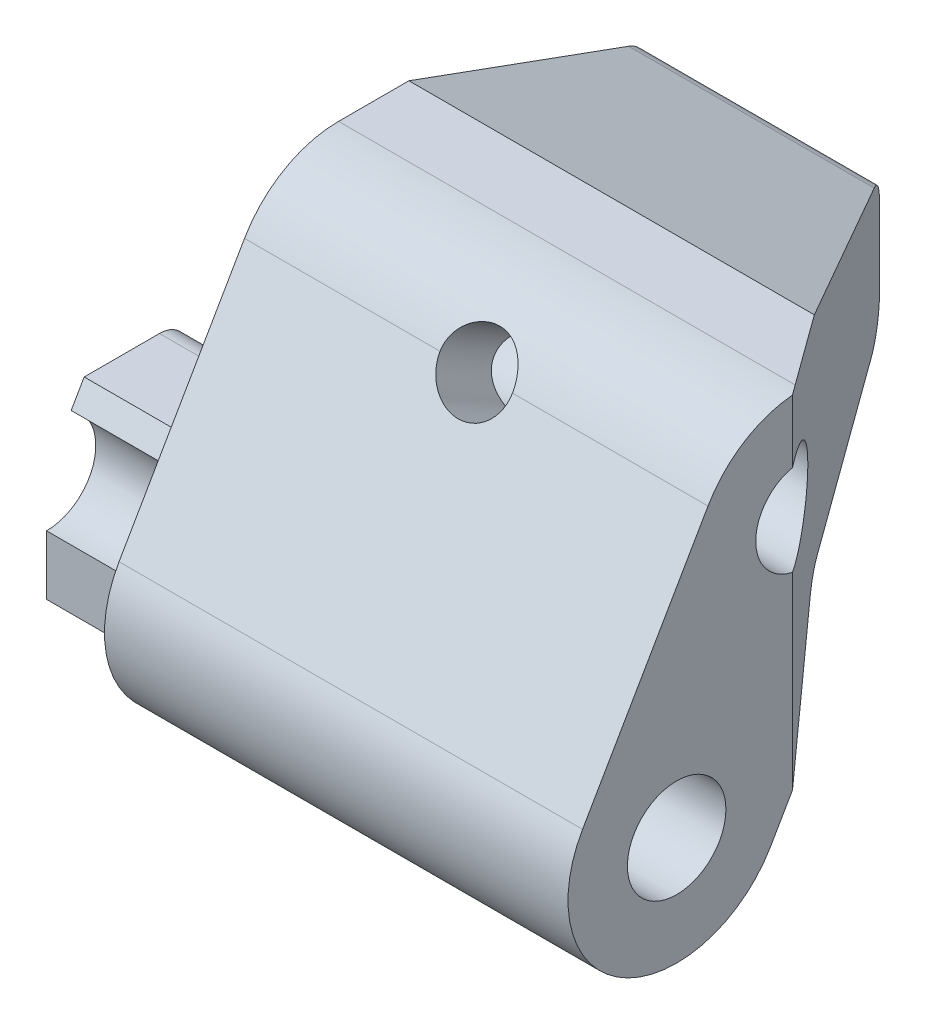
SolidWorks part; units mm, degrees
ref_plane "Front Plane" through (0, 0, 0) normal (0, 0, 1) x (1, 0, 0)
ref_plane "Top Plane" through (0, 0, 0) normal (0, 1, 0) x (1, 0, 0)
ref_plane "Right Plane" through (0, 0, 0) normal (1, 0, 0) x (0, 0, -1)
sketch "Sketch1" plane through (0, 0, 0) normal (1, 0, 0) x (0, 0, -1)
  line L0 (-3.2476, 1.875) -> (1.0825, 9.375)
  line L1 (0, 0) -> (4.3301, 7.5) construction
  line L2 (4.3301, 7.5) -> (15, 7.5) construction
  line L3 (0, 0) -> (5.1213, 0) construction
  line L4 (4.3301, 11.25) -> (15, 11.25)
  line L5 (15, 11.25) -> (15, 3.75)
  line L6 (15, 3.75) -> (6.4952, 3.75)
  line L7 (6.4952, 3.75) -> (3.2476, -1.875)
  circle A0 centre (0, 0) radius 1.7
  arc A1 (-3.2476, 1.875) -> (3.2476, -1.875) centre (0, 0) ccw
  circle A2 centre (4.3301, 7.5) radius 1.6
  arc A3 (1.0825, 9.375) -> (4.3301, 11.25) centre (4.3301, 7.5) cw
  dimension "D1" = 3.4
  dimension "D6" = 3.2
  dimension "D2" = 15
  dimension "D3" = 7.5
  dimension "D4" = 60
  dimension "D5" = 7.5
  dimension "D7" = 7.5
extrude "Boss-Extrude1" add sketch "Sketch1" along normal blind 22
sketch "Sketch2" plane through (0, 0, 0) normal (-1, 0, 0) x (0, 0, 1)
  line L0 (0, 0) -> (-4.3301, 7.5) construction
  line L1 (-4.3301, 7.5) -> (-12.9879, 7.5) construction
  line L2 (-15, 11.25) -> (5.3287, 11.25)
  line L3 (5.3287, 11.25) -> (5.3287, -6.2558)
  line L4 (5.3287, -6.2558) -> (0, -6.2558)
  line L5 (0, -6.2558) -> (0, 0)
  line L6 (0, 0) -> (-1.299, 2.25)
  line L7 (-1.299, 2.25) -> (-5.6292, 2.25)
  line L8 (-3.2476, -1.875) -> (-6.4952, 3.75) construction
  line L9 (-5.6292, 2.25) -> (-15, 2.25)
  line L10 (-15, 2.25) -> (-15, 11.25)
  dimension "D1" = 5.25
extrude "Cut-Extrude1" cut sketch "Sketch2" against normal blind 6
sketch "Sketch3" plane through (0, 0, -15) normal (0, 0, -1) x (-1, 0, 0)
  line L0 (-19.5, 3.75) -> (-19.5, 5.15)
  line L2 (-22, 3.75) -> (-6, 3.75) construction
  line L3 (-17.9, 6.75) -> (-10.1, 6.75)
  line L6 (-10.1, 6.75) -> (-6, 6.75)
  line L7 (-8.5, 3.75) -> (-19.5, 3.75)
  line L8 (-14, 6.75) -> (-14, 3.75) construction
  line L9 (-22, 3.75) -> (-22, 11.25) construction
  line L10 (-6, 11.25) -> (-6, 3.75) construction
  line L11 (-6, 6.75) -> (-6, 3.75)
  line L12 (-6, 3.75) -> (-8.5, 3.75)
  arc A0 (-19.5, 5.15) -> (-17.9, 6.75) centre (-17.9, 5.15) cw
  dimension "D1" = 1.6
  dimension "D2" = 3
  dimension "D3" = 11
  dimension "D4" = 8
extrude "Cut-Extrude2" cut sketch "Sketch3" against normal blind 5 from offset 2 offset against normal yes
chamfer "Chamfer1" distance 3 angle 70 1 edges at (14, 11.25, -15)
sketch "Sketch4" plane through (6, 0, 0) normal (-1, 0, 0) x (0, 0, 1)
  circle A0 centre (-4.3301, 7.5) radius 1.6
  circle A1 centre (-4.3301, 7.5) radius 2.2
  circle A2 centre (-4.3301, 7.5) radius 1.6 construction
  dimension "D1" = 0.6
extrude "Boss-Extrude2" add sketch "Sketch4" along normal blind 0.15
sketch "Sketch5" plane through (0, 0, 0) normal (-1, 0, 0) x (0, 0, 1)
  circle A0 centre (0, 0) radius 7.371
extrude "Cut-Extrude3" cut sketch "Sketch5" against normal blind 0.25
fillet "Fillet1" radius 1 4 edges at (14, 3.75, -6.4952) (14, 3.75, -15) (14, 8.25, -15) (3.125, 2.25, -5.6292)
sketch "Sketch7" plane through (0, 0, 0) normal (0, 1, 0) x (1, 0, 0)
  line L0 (22, 4) -> (14, 15)
  line L1 (22, 1.0825) -> (22, 4.3301) construction
  line L3 (14, 15) -> (22, 15)
  line L4 (22, 15) -> (22, 4)
  dimension "D1" = 8
  dimension "D2" = 11
extrude "Cut-Extrude4" cut sketch "Sketch7" against normal through all both and the other way through all
sketch "Sketch8" plane through (16.2919, 0, -11.8486) normal (0.8087, 0, -0.5882) x (-0.5882, 0, -0.8087)
  line L0 (-5.3399, 3.75) -> (2.6601, 3.75)
  line L1 (2.6601, 3.75) -> (2.6601, 6.75)
  line L2 (2.6601, 6.75) -> (-5.3399, 6.75)
  line L3 (-5.3399, 6.75) -> (-5.3399, 3.75)
  line L4 (-4.7588, 3.75) -> (-5.9056, 3.75) construction
  line L5 (1.4236, 6.75) -> (-2.7341, 6.75) construction
  dimension "D1" = 8
extrude "Boss-Extrude4" add sketch "Sketch8" against normal blind 1
sketch "Sketch10" plane through (0, 1.875, 3.2476) normal (0, 0.5, 0.866) x (1, 0, 0)
  line L0 (22, 8.6603) -> (6, 8.6603) construction
  circle A0 centre (14, 8.6603) radius 1.25
  dimension "D1" = 2.5
extrude "Cut-Extrude7" cut sketch "Sketch10" against normal blind 4
sketch "Sketch11" plane through (6, 0, 0) normal (-1, 0, 0) x (0, 0, 1)
  line L1 (-13, 6.75) -> (-8, 6.75)
  line L2 (-13, 6.75) -> (-13, 3.75)
  line L3 (-13, 3.75) -> (-8, 3.75)
  line L4 (-8, 6.75) -> (-8, 3.75)
extrude "Boss-Extrude5" add sketch "Sketch11" against normal blind 1
